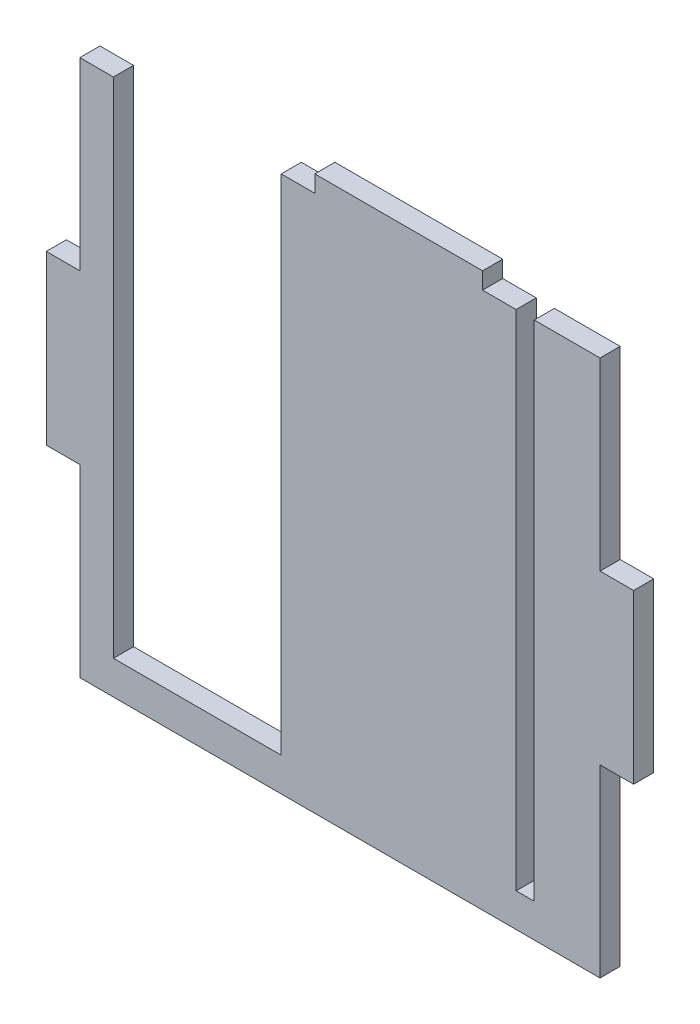
SolidWorks part; units mm, degrees
ref_plane "Front Plane" through (0, 0, 0) normal (0, 0, 1) x (1, 0, 0)
ref_plane "Top Plane" through (0, 0, 0) normal (0, 1, 0) x (1, 0, 0)
ref_plane "Right Plane" through (0, 0, 0) normal (1, 0, 0) x (0, 0, -1)
sketch "Sketch1" plane through (0, 0, 0) normal (0, 0, 1) x (1, 0, 0)
  line L1 (0, 0) -> (-155, 0)
  line L2 (0, 0) -> (0, 160)
  line L3 (0, 160) -> (-155, 160)
  line L4 (-155, 0) -> (-155, 160)
  line L6 (0, 80) -> (-155, 80) construction
  line L7 (-77.647, 160) -> (-72.6112, 160)
  line L13 (-19.6, 160) -> (-25, 160)
  line L14 (-19.6, 160) -> (-19.6, 10)
  line L15 (-19.6, 10) -> (-25, 10)
  line L16 (-25, 160) -> (-25, 10)
  line L17 (-22.3, 10) -> (-22.3, 160) construction
  line L18 (-19.6, 85) -> (-25, 85) construction
  line L19 (-85, 160) -> (-35, 160)
  line L20 (-85, 160) -> (-85, 165)
  line L21 (-85, 165) -> (-35, 165)
  line L22 (-35, 160) -> (-35, 165)
  line L24 (-85, 162.5) -> (-35, 162.5) construction
  line L25 (-155, 105) -> (-165, 105)
  line L26 (-155, 105) -> (-155, 55)
  line L27 (-155, 55) -> (-165, 55)
  line L28 (-165, 105) -> (-165, 55)
  line L29 (-160, 55) -> (-160, 105) construction
  line L30 (-155, 80) -> (-165, 80) construction
  line L31 (0, 105) -> (10, 105)
  line L32 (0, 105) -> (0, 55)
  line L33 (0, 55) -> (10, 55)
  line L34 (10, 105) -> (10, 55)
  line L35 (5, 55) -> (5, 105) construction
  line L36 (0, 80) -> (10, 80) construction
  line L39 (-145, 160) -> (-95, 160)
  line L40 (-145, 160) -> (-145, 10)
  line L41 (-145, 10) -> (-95, 10)
  line L42 (-95, 160) -> (-95, 10)
  line L43 (-120, 10) -> (-120, 160) construction
  line L44 (-145, 85) -> (-95, 85) construction
  point P104 (-160, 80)
  point P136 (-65.1291, 93.1887)
  point P145 (-22.3, 85)
  point P155 (5, 80)
  point P196 (-60, 80)
  point P248 (-60, 162.5)
  point P294 (-120, 85)
  dimension "D1" = 5
  dimension "D2" = 10
  dimension "D3" = 10
  dimension "D4" = 50
  dimension "D5" = 10
  dimension "D6" = 5.4
  dimension "D7" = 150
  dimension "D8" = 10
  dimension "D9" = 50
  dimension "D10" = 50
  dimension "D11" = 19.6
  dimension "D12" = 50
  dimension "D13" = 10
  dimension "D14" = 10
extrude "Boss-Extrude1" add sketch "Sketch1" along normal blind 6
